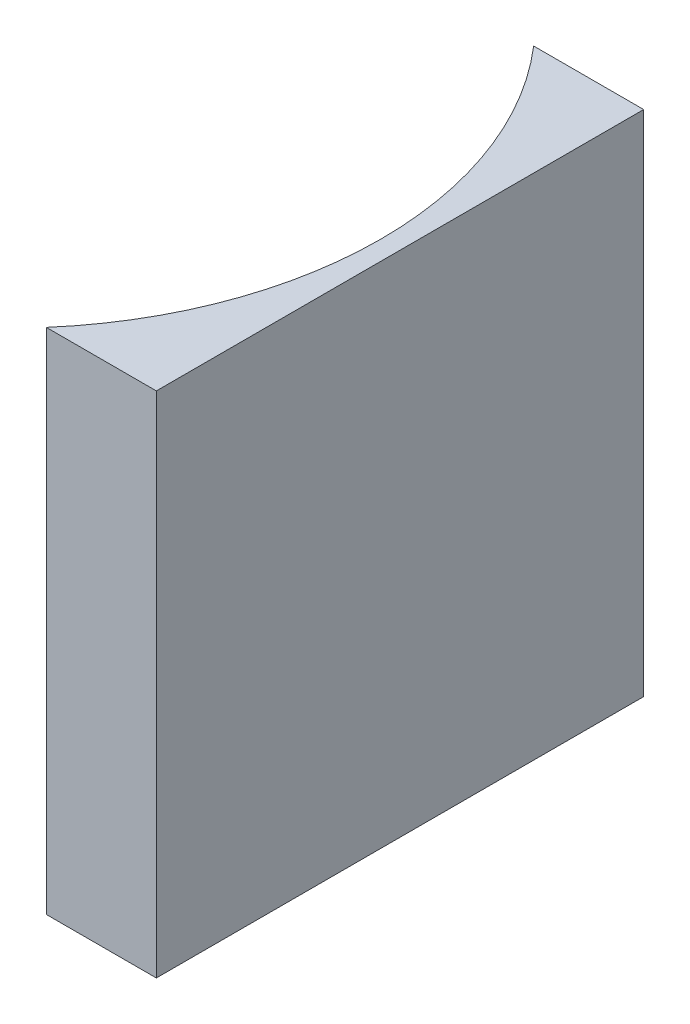
SolidWorks part; units mm, degrees
ref_plane "前视基准面" through (0, 0, 0) normal (0, 0, 1) x (1, 0, 0)
ref_plane "上视基准面" through (0, 0, 0) normal (0, 1, 0) x (1, 0, 0)
ref_plane "右视基准面" through (0, 0, 0) normal (1, 0, 0) x (0, 0, -1)
sketch "草图1" plane through (0, 0, 0) normal (0, 1, 0) x (1, 0, 0)
  line L0 (0, 0) -> (0, -50.8)
  line L1 (0, 0) -> (-11.4695, 0)
  line L2 (0, -50.8) -> (-11.4695, -50.8)
  line L3 (8.2336, -25.4) -> (-10.4405, -25.4) construction
  arc A0 (-11.4695, -50.8) -> (-11.4695, 0) centre (-40.8, -25.4) ccw
  point P7 (-2, -25.4)
  point P8 (0, -25.4)
  dimension "D2" = 38.8
  dimension "D3" = 2
  dimension "D1" = 50.8
extrude "凸台-拉伸1" add sketch "草图1" along normal blind 53
